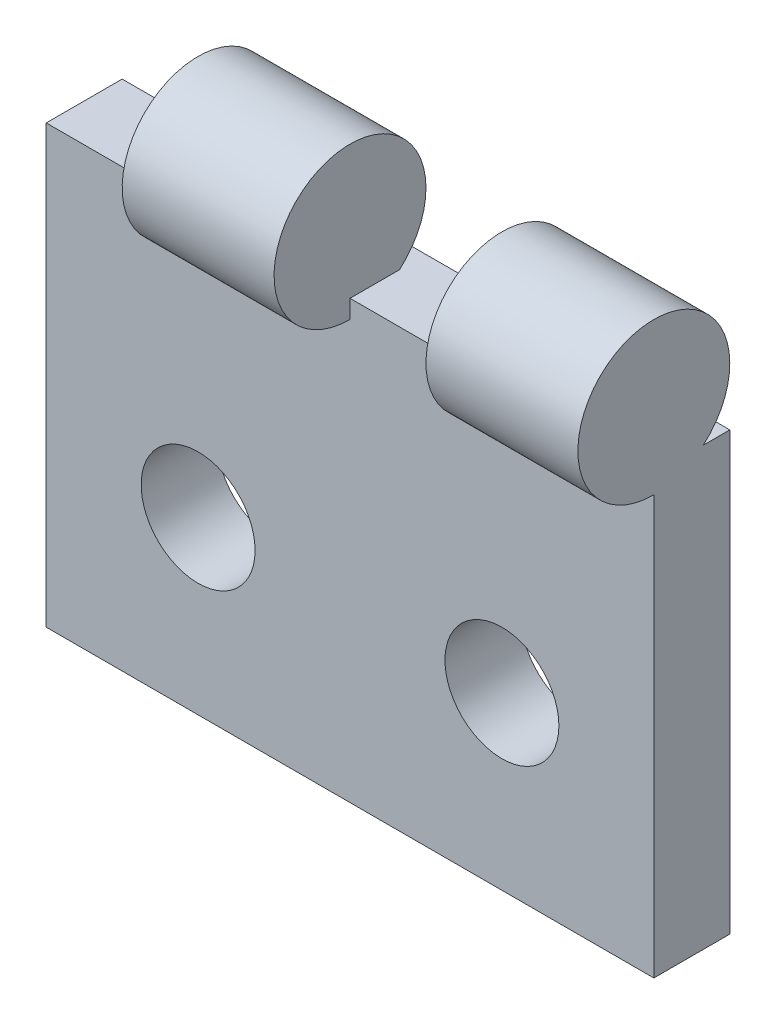
SolidWorks part; units mm, degrees
ref_plane "Front" through (0, 0, 0) normal (0, 0, 1) x (1, 0, 0)
ref_plane "Top" through (0, 0, 0) normal (0, 1, 0) x (1, 0, 0)
ref_plane "Right" through (0, 0, 0) normal (1, 0, 0) x (0, 0, -1)
sketch "Sketch1" plane through (0, 0, 0) normal (0, 0, 1) x (1, 0, 0)
  line L0 (0, 11.5) -> (0, 14.5) construction
  line L1 (0, 0) -> (16, 0)
  line L2 (0, 0) -> (0, 11.5)
  line L3 (0, 11.5) -> (16, 11.5)
  line L4 (16, 0) -> (16, 11.5)
  line L5 (0, 14.5) -> (16, 14.5) construction
  line L6 (16, 14.5) -> (16, 11.5) construction
  dimension "D1" = 16
  dimension "D2" = 14.5
  dimension "D3" = 3
extrude "Boss-Extrude1" add sketch "Sketch1" along normal blind 2
sketch "Sketch2" plane through (16, 0, 0) normal (1, 0, 0) x (0, 0, -1)
  line L0 (0, 11.5) -> (0, 13.0179) construction
  circle A0 centre (-2, 13.0179) radius 2
  point P6 (0, 0)
  dimension "D1" = 4
extrude "Boss-Extrude2" add sketch "Sketch2" against normal blind 4
pattern_linear "LPattern1" count 2 spacing 8 along (-1, 0, 0) of "Boss-Extrude2"
hole_wizard "Ø3.0mm Dowel Hole1" positions "Sketch3" profile "Sketch4" hole size "Ø3.0" standard "ANSI Metric" end condition through all
sketch "Sketch3" plane through (0, 0, 2) normal (0, 0, 1) x (1, 0, 0)
  line L0 (0, 11.5) -> (0, 0) construction
  line L1 (16, 0) -> (16, 11.0179) construction
  line L2 (12, 11.5) -> (8, 11.5) construction
  point P0 (4, 4.5)
  point P2 (12, 4.5)
  point P11 (0, 0)
  dimension "D1" = 4
  dimension "D2" = 4
  dimension "D3" = 7
sketch "Sketch4" plane through (4, 4.5, 2) normal (1, 0, 0) x (0, -1, 0)
  line L0 (0, 0) -> (0, 2)
  line L1 (0, 2) -> (1.5, 2)
  line L2 (1.5, 2) -> (1.5, 0)
  line L5 (1.5, 0) -> (0, 0)
  line L11 (0, -6.35) -> (0, 107.95) construction
  dimension "Thru Hole Dia." = 3
  dimension "Thru Hole Depth" = 2
